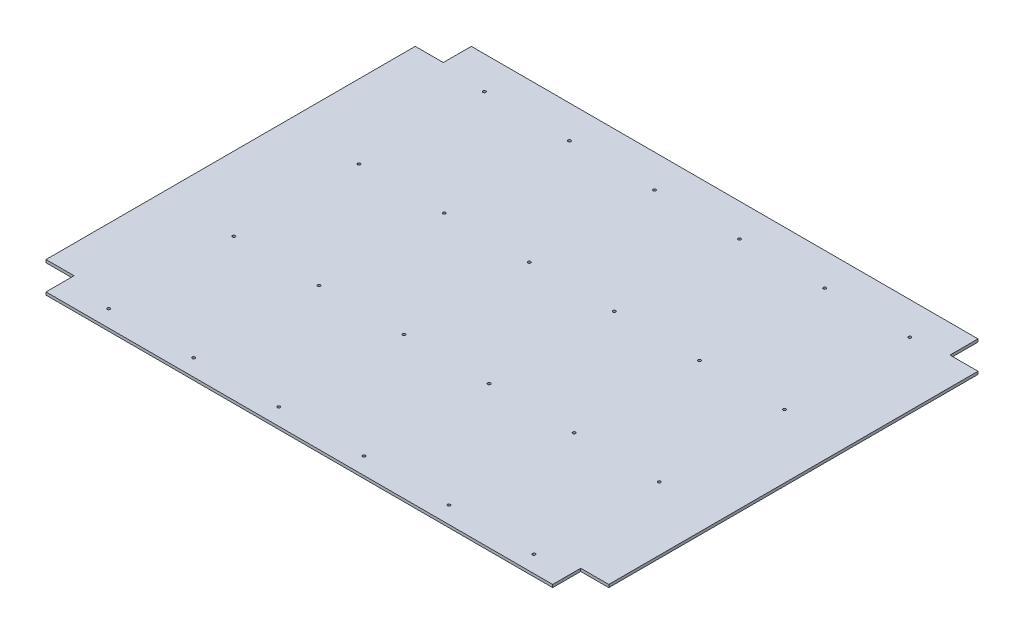
SolidWorks part; units mm, degrees
ref_plane "Front" through (0, 0, 0) normal (0, 0, 1) x (1, 0, 0)
ref_plane "Top" through (0, 0, 0) normal (0, 1, 0) x (1, 0, 0)
ref_plane "Right" through (0, 0, 0) normal (1, 0, 0) x (0, 0, -1)
sketch "Sketch1" plane through (0, 0, 0) normal (0, 1, 0) x (1, 0, 0)
  line L1 (0, 0) -> (542, 0)
  line L2 (0, 0) -> (0, 455)
  line L3 (0, 455) -> (542, 455)
  line L4 (542, 0) -> (542, 455)
  circle A0 centre (49, 18) radius 1.5
  circle A1 centre (140, 18) radius 1.5
  circle A2 centre (231, 18) radius 1.5
  circle A3 centre (413, 18) radius 1.5
  circle A4 centre (504, 18) radius 1.5
  circle A5 centre (322, 18) radius 1.5
  circle A6 centre (49, 152) radius 1.5
  circle A7 centre (140, 152) radius 1.5
  circle A8 centre (231, 152) radius 1.5
  circle A9 centre (322, 152) radius 1.5
  circle A10 centre (413, 152) radius 1.5
  circle A11 centre (504, 152) radius 1.5
  circle A12 centre (49, 286) radius 1.5
  circle A13 centre (140, 286) radius 1.5
  circle A14 centre (231, 286) radius 1.5
  circle A15 centre (322, 286) radius 1.5
  circle A16 centre (413, 286) radius 1.5
  circle A17 centre (504, 286) radius 1.5
  circle A18 centre (49, 420) radius 1.5
  circle A19 centre (140, 420) radius 1.5
  circle A20 centre (231, 420) radius 1.5
  circle A21 centre (322, 420) radius 1.5
  circle A22 centre (413, 420) radius 1.5
  circle A23 centre (504, 420) radius 1.5
  dimension "D1" = 18
  dimension "D2" = 49
  dimension "D3" = 91
  dimension "D4" = 91
  dimension "D5" = 91
  dimension "D6" = 91
  dimension "D7" = 38
  dimension "D8" = 134
  dimension "D9" = 134
  dimension "D10" = 134
extrude "Boss-Extrude1" add sketch "Sketch1" along normal blind 3
sketch "Sketch2" plane through (0, 0, 0) normal (0, 1, 0) x (1, 0, 0)
  line L1 (0, 30) -> (-30, 30)
  line L2 (0, 30) -> (0, 425)
  line L3 (0, 425) -> (-30, 425)
  line L4 (-30, 30) -> (-30, 425)
  line L5 (542, 30) -> (572, 30)
  line L6 (542, 30) -> (542, 425)
  line L7 (542, 425) -> (572, 425)
  line L8 (572, 30) -> (572, 425)
extrude "Boss-Extrude2" add sketch "Sketch2" along normal blind 3
